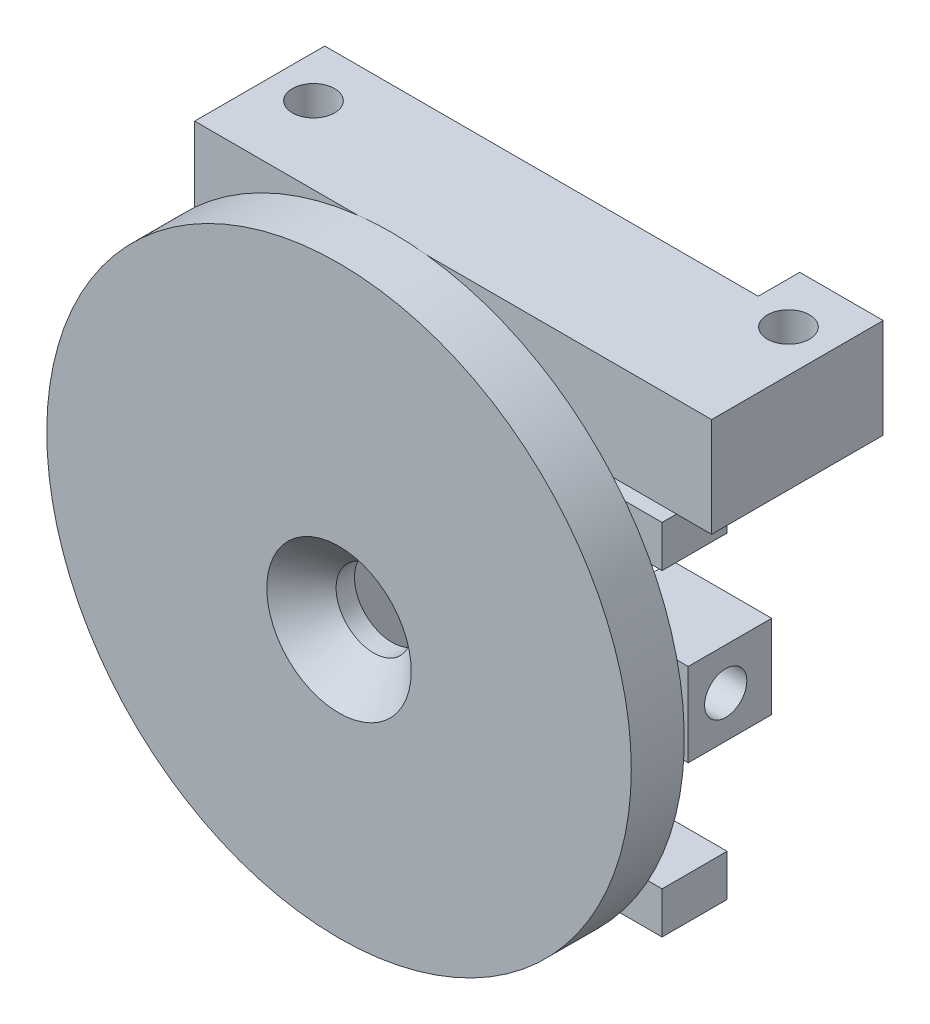
SolidWorks part; units mm, degrees
ref_plane "Front Plane" through (0, 0, 0) normal (0, 0, 1) x (1, 0, 0)
ref_plane "Top Plane" through (0, 0, 0) normal (0, 1, 0) x (1, 0, 0)
ref_plane "Right Plane" through (0, 0, 0) normal (1, 0, 0) x (0, 0, -1)
sketch "Sketch1" plane through (0, 0, 0) normal (0, 0, 1) x (1, 0, 0)
  circle A31 centre (0, 0) radius 35
  dimension "D1" = 70
extrude "Boss-Extrude1" add sketch "Sketch1" along normal blind 6.35
sketch "Sketch2" plane through (0, 0, 0) normal (0, 0, -1) x (-1, 0, 0)
  line L0 (-12.7, 34.75) -> (12.7, 34.75)
  line L2 (-12.7, 34.75) -> (-12.7, -34.75)
  line L3 (-12.7, -34.75) -> (12.7, -34.75)
  line L4 (12.7, 34.75) -> (12.7, -34.75)
  line L5 (-7.35, 23.4) -> (7.35, 23.4)
  line L6 (-7.35, 23.4) -> (-7.35, -29.4)
  line L7 (-7.35, -29.4) -> (7.35, -29.4)
  line L8 (7.35, 23.4) -> (7.35, -29.4)
  point P8 (-12.7, 0)
  point P13 (0, -34.75)
  dimension "D3" = 14.7
  dimension "D1" = 69.5
  dimension "D2" = 25.4
  dimension "D4" = 5.35
  dimension "D5" = 5.35
  dimension "D6" = 52.8
extrude "Boss-Extrude2" add sketch "Sketch2" along normal blind 15.5784
hole_wizard "CSK for M8 Flat Head Machine Screw1" positions "Sketch3" profile "Sketch4" countersink size "M8" standard "ANSI Metric"
sketch "Sketch3" plane through (0, 0, 6.35) normal (0, 0, 1) x (1, 0, 0)
  point P5 (0, -3)
  dimension "D1" = 3
sketch "Sketch4" plane through (0, -3, 6.35) normal (1, 0, 0) x (0, -1, 0)
  line L0 (0, 0) -> (0, 20.2039)
  line L1 (0, 20.2039) -> (4.5, 17.5)
  line L2 (4.5, 17.5) -> (4.5, 4.15)
  line L3 (4.5, 4.15) -> (8.65, 0)
  line L5 (8.65, 0) -> (0, 0)
  line L6 (-4.5, 4.15) -> (-8.65, 0) construction
  line L10 (0, 20.2039) -> (-4.5, 17.5) construction
  line L11 (0, -6.35) -> (0, 107.95) construction
  dimension "Hole Dia." = 9
  dimension "Hole Depth" = 17.5
  dimension "Near C'Sink Dia." = 17.3
  dimension "Near C'Sink Angle" = 90
  dimension "Drill Angle" = 118
sketch "Sketch6" plane through (12.7, 0, 0) normal (1, 0, 0) x (0, 0, -1)
  line L0 (15.5784, 34.75) -> (15.5784, -34.75) construction
  line L1 (0, 34.75) -> (15.5784, 34.75)
  line L2 (0, 34.75) -> (0, 22.85)
  line L3 (0, 22.85) -> (15.5784, 22.85)
  line L4 (15.5784, 34.75) -> (15.5784, 22.85)
  dimension "D1" = 11.9
extrude "Boss-Extrude3" add sketch "Sketch6" along normal blind 25.5721
sketch "Sketch7" plane through (-12.7, 0, 0) normal (-1, 0, 0) x (0, 0, 1)
  line L1 (-15.5784, 34.75) -> (0, 34.75)
  line L2 (-15.5784, 34.75) -> (-15.5784, 22.85)
  line L3 (-15.5784, 22.85) -> (0, 22.85)
  line L4 (0, 34.75) -> (0, 22.85)
  dimension "D1" = 11.9
extrude "Boss-Extrude4" add sketch "Sketch7" along normal blind 10.9373
sketch "Sketch8" plane through (0, 34.75, 0) normal (0, 1, 0) x (1, 0, 0)
  line L1 (-23.6373, 0) -> (-23.6373, 15.5784) construction
  line L3 (-23.6373, 15.5784) -> (38.2721, 15.5784) construction
  circle A0 centre (-18.6373, 9.2284) radius 2.5273
  dimension "D1" = 5.0546
  dimension "D2" = 6.35
  dimension "D3" = 5
extrude "Cut-Extrude1" cut sketch "Sketch8" against normal blind 7
sketch "Sketch9" plane through (0, 0, -15.5784) normal (0, 0, -1) x (-1, 0, 0)
  line L1 (-38.2721, 34.75) -> (-28.2721, 34.75)
  line L2 (-38.2721, 34.75) -> (-38.2721, 22.85)
  line L3 (-38.2721, 22.85) -> (-28.2721, 22.85)
  line L4 (-28.2721, 34.75) -> (-28.2721, 22.85)
  dimension "D1" = 10
extrude "Boss-Extrude5" add sketch "Sketch9" along normal blind 4.9727
sketch "Sketch10" plane through (0, 34.75, 0) normal (0, 1, 0) x (1, 0, 0)
  line L0 (38.2721, 20.5511) -> (38.2721, 0) construction
  line L1 (28.2721, 20.5511) -> (38.2721, 20.5511) construction
  circle A0 centre (33.2721, 14.2011) radius 2.5273
  circle A1 centre (-18.6373, 9.2284) radius 2.5273 construction
  dimension "D1" = 5
  dimension "D2" = 6.35
extrude "Cut-Extrude2" cut sketch "Sketch10" against normal blind 7
sketch "Sketch11" plane through (12.7, 0, 0) normal (1, 0, 0) x (0, 0, -1)
  line L0 (15.5784, 22.85) -> (15.5784, -34.75) construction
  line L1 (15.5784, -3.175) -> (20.9169, -3.175)
  line L2 (15.5784, -3.175) -> (15.5784, -13.175)
  line L3 (15.5784, -13.175) -> (20.9169, -13.175)
  line L4 (20.9169, -3.175) -> (20.9169, -13.175)
  line L5 (0, 22.85) -> (20.5511, 22.85) construction
  dimension "D1" = 26.025
  dimension "D2" = 10
  dimension "D3" = 5.3384
extrude "Boss-Extrude6" add sketch "Sketch11" against normal up to surface (5.35 mm away) up to face at (7.35, -3, -7.7892)
sketch "Sketch12" plane through (12.7, 0, 0) normal (1, 0, 0) x (0, 0, -1)
  line L0 (15.5784, -13.175) -> (20.9169, -13.175) construction
  line L1 (20.9169, -3.175) -> (10.9169, -3.175)
  line L2 (20.9169, -3.175) -> (20.9169, -13.175)
  line L3 (20.9169, -13.175) -> (10.9169, -13.175)
  line L4 (10.9169, -3.175) -> (10.9169, -13.175)
  line L5 (15.5784, 22.85) -> (15.5784, -3.175) construction
  line L6 (15.5784, 13.325) -> (7.7892, 13.325)
  line L7 (15.5784, 13.325) -> (15.5784, 8.325)
  line L8 (15.5784, 8.325) -> (7.7892, 8.325)
  line L9 (7.7892, 13.325) -> (7.7892, 8.325)
  line L10 (15.5784, -13.175) -> (15.5784, -34.75) construction
  line L11 (15.5784, -24.675) -> (7.7892, -24.675)
  line L12 (15.5784, -24.675) -> (15.5784, -29.675)
  line L13 (15.5784, -29.675) -> (7.7892, -29.675)
  line L14 (7.7892, -24.675) -> (7.7892, -29.675)
  point P13 (20.9169, -8.175)
  dimension "D1" = 10
  dimension "D2" = 21.5
  dimension "D3" = 7.7892
  dimension "D4" = 5
  dimension "D5" = 43
  dimension "D6" = 5
extrude "Boss-Extrude7" add sketch "Sketch12" along normal blind 11.85
sketch "Sketch13" plane through (24.55, 0, 0) normal (1, 0, 0) x (0, 0, -1)
  line L0 (10.9169, -3.175) -> (10.9169, -13.175) construction
  line L1 (10.9169, -13.175) -> (20.9169, -13.175) construction
  circle A0 centre (15.4092, -8.175) radius 2.5273
  dimension "D1" = 4.4924
  dimension "D3" = 5.0546
  dimension "D2" = 5
extrude "Cut-Extrude3" cut sketch "Sketch13" against normal blind 7
sketch "Sketch14" plane through (0, 0, -20.9169) normal (0, 0, -1) x (-1, 0, 0)
  line L6 (-12.7, -3.175) -> (-7.35, -3.175)
  line L7 (-12.7, -3.175) -> (-12.7, -13.175)
  line L8 (-12.7, -13.175) -> (-7.35, -13.175)
  line L9 (-7.35, -3.175) -> (-7.35, -13.175)
extrude "Cut-Extrude4" cut sketch "Sketch14" against normal up to surface (5.3384 mm away) up to face at (8.2654, -0.7792, -15.5784)
